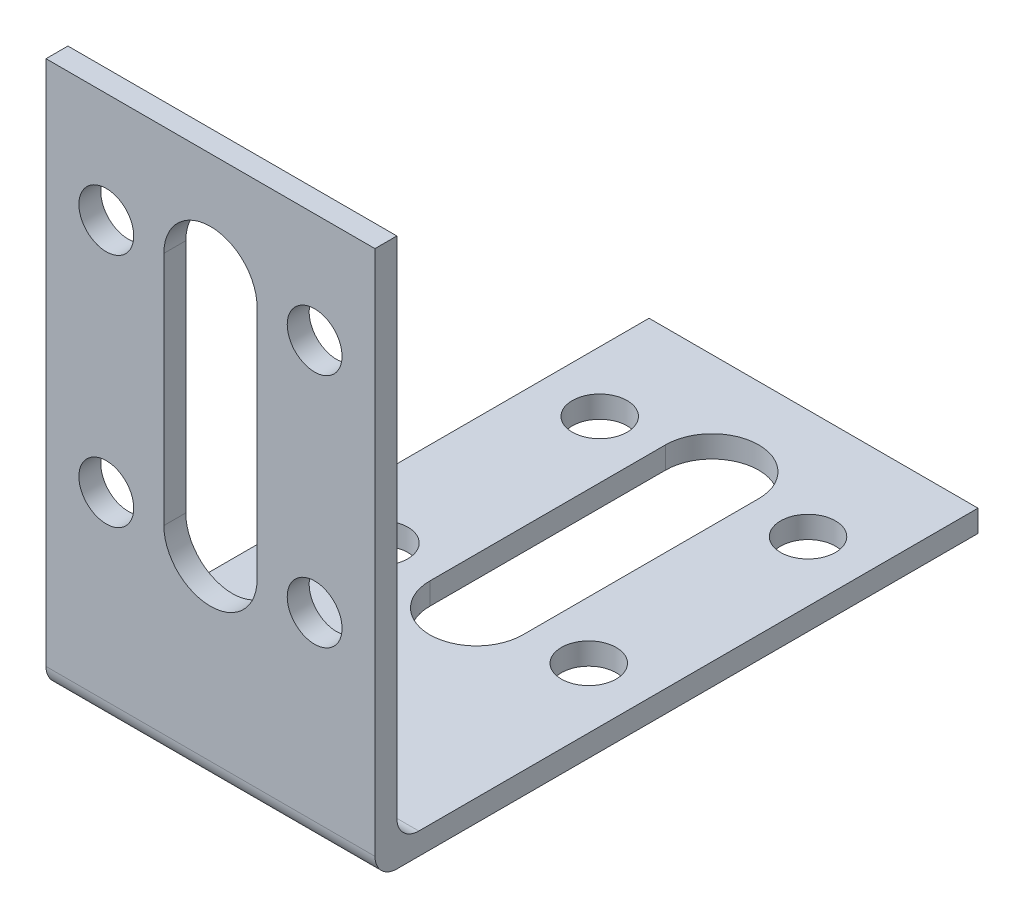
SolidWorks part; units mm, degrees
material "AISI 1020"
ref_plane "Plan de face" through (0, 0, 0) normal (0, 0, 1) x (1, 0, 0)
ref_plane "Plan de dessus" through (0, 0, 0) normal (0, 1, 0) x (1, 0, 0)
ref_plane "Plan de droite" through (0, 0, 0) normal (1, 0, 0) x (0, 0, -1)
sketch "Esquisse1" plane through (0, 0, 0) normal (1, 0, 0) x (0, 0, -1)
  line L0 (0, 0) -> (0, 50)
  line L1 (0, 50) -> (2, 50)
  line L2 (2, 50) -> (2, 2)
  line L3 (2, 2) -> (55, 2)
  line L4 (55, 2) -> (55, 0)
  line L5 (55, 0) -> (0, 0)
  dimension "D1" = 2
  dimension "D2" = 2
  dimension "D3" = 50
  dimension "D4" = 55
extrude "Boss.-Extru.1" add sketch "Esquisse1" along normal mid plane 30
fillet "Congé1" radius 2 2 edges at (0, 0, 0) (0, 2, -2)
sketch "Esquisse2" plane through (0, 2, 0) normal (0, 1, 0) x (1, 0, 0)
  line L0 (0, 24.25) -> (0, 45.75) construction
  line L1 (-4.25, 24.25) -> (-4.25, 45.75)
  line L2 (4.25, 24.25) -> (4.25, 45.75)
  line L4 (15, 55) -> (-15, 55) construction
  line L5 (15, 55) -> (15, 4) construction
  line L6 (-15, 35) -> (15, 35) construction
  line L8 (-15, 55) -> (-15, 4) construction
  line L9 (0, 55) -> (0, 2) construction
  line L10 (15, 2) -> (-15, 2) construction
  arc A0 (-4.25, 24.25) -> (4.25, 24.25) centre (0, 24.25) ccw
  arc A1 (4.25, 45.75) -> (-4.25, 45.75) centre (0, 45.75) ccw
  circle A2 centre (9.5, 45) radius 2.5
  circle A3 centre (9.5, 25) radius 2.5
  circle A4 centre (9.5, 45) radius 2.5
  circle A5 centre (9.5, 25) radius 2.5
  circle A6 centre (-9.5, 45) radius 2.5
  circle A7 centre (-9.5, 25) radius 2.5
  point P3 (0, 35)
  dimension "D1" = 4.25
  dimension "D6" = 5
  dimension "D2" = 21.5
  dimension "D3" = 9.25
  dimension "D4" = 10
  dimension "D5" = 5.5
extrude "Enlèv. mat.-Extru.1" cut sketch "Esquisse2" against normal up to next contours L2 A1 L1 A0 | A7 | A6 | A2 | A3
sketch "Esquisse3" plane through (0, 0, -2) normal (0, 0, -1) x (-1, 0, 0)
  line L0 (0, 40) -> (0, 18.5) construction
  line L1 (4.25, 40) -> (4.25, 18.5)
  line L2 (-4.25, 40) -> (-4.25, 18.5)
  line L3 (-15, 4) -> (-15, 50) construction
  line L4 (-15, 29.25) -> (15, 29.25) construction
  line L6 (0, 4) -> (0, 50) construction
  line L7 (-15, 4) -> (15, 4) construction
  line L8 (-15, 50) -> (15, 50) construction
  arc A0 (4.25, 40) -> (-4.25, 40) centre (0, 40) ccw
  arc A1 (-4.25, 18.5) -> (4.25, 18.5) centre (0, 18.5) ccw
  circle A2 centre (-9.5, 18.5) radius 2.5
  circle A3 centre (-9.5, 40) radius 2.5
  circle A4 centre (-9.5, 18.5) radius 2.5
  circle A5 centre (-9.5, 40) radius 2.5
  circle A6 centre (9.5, 40) radius 2.5
  circle A7 centre (9.5, 18.5) radius 2.5
  point P3 (0, 29.25)
  dimension "D1" = 4.25
  dimension "D3" = 5
  dimension "D2" = 21.5
  dimension "D4" = 5.5
  dimension "D5" = 10
  dimension "D6" = 10
extrude "Enlèv. mat.-Extru.2" cut sketch "Esquisse3" against normal up to next contours L2 A1 L1 A0 | A3 | A6 | A7 | A2
